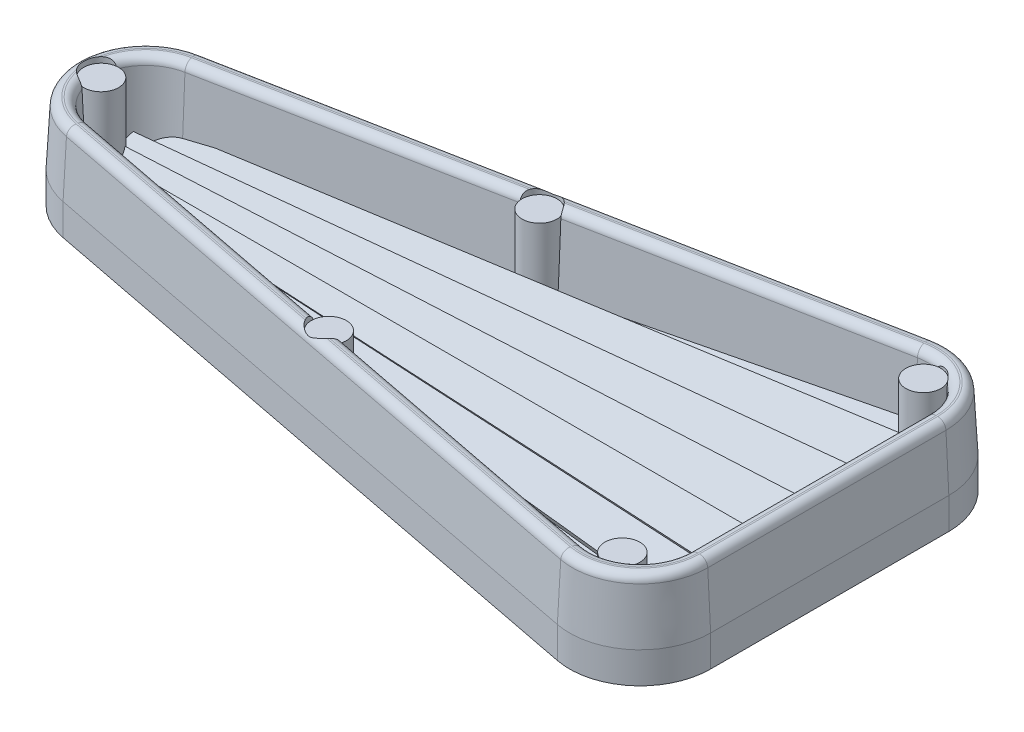
SolidWorks part; units mm, degrees
ref_plane "Front Plane" through (0, 0, 0) normal (0, 0, 1) x (1, 0, 0)
ref_plane "Top Plane" through (0, 0, 0) normal (0, 1, 0) x (1, 0, 0)
ref_plane "Right Plane" through (0, 0, 0) normal (1, 0, 0) x (0, 0, -1)
sketch "Sketch1" plane through (0, 0, 0) normal (0, 1, 0) x (1, 0, 0)
  line L0 (24.0776, 4.6752) -> (65.4796, 12.7143)
  line L1 (0, 0) -> (148.2111, 0) construction
  line L2 (71.1498, 8.0391) -> (71.1498, -8.0391)
  line L3 (24.0776, -4.6752) -> (65.4796, -12.7143)
  line L4 (0, 0) -> (85.7563, 4.4943) construction
  line L5 (0, 0) -> (80.0927, 8.4181) construction
  line L6 (0, 0) -> (103.5127, 16.3948) construction
  arc A0 (24.0776, 4.6752) -> (24.0776, -4.6752) centre (24.9853, 0) ccw
  arc A1 (71.1498, -8.0391) -> (65.4796, -12.7143) centre (66.3873, -8.0391) cw
  arc A2 (71.1498, 8.0391) -> (65.4796, 12.7143) centre (66.3873, 8.0391) ccw
  point P12 (71.1498, 0)
  dimension "D1" = 4.7625
  dimension "D2" = 4.7625
  dimension "D3" = 50.927
  dimension "D4" = 25.6032
  dimension "D5" = 3
  dimension "D6" = 6
  dimension "D7" = 9
extrude "Boss-Extrude1" add sketch "Sketch1" along normal blind 3.4544
sketch "Sketch2" plane through (0, 0, 0) normal (1, 0, 0) x (0, 0, -1)
  line L0 (0, 0) -> (0, 5.5486) construction
  line L1 (-1.905, 3.4544) -> (0, 1.5494)
  line L2 (-8.0391, 3.4544) -> (8.0391, 3.4544) construction
  line L3 (1.905, 3.4544) -> (0, 1.5494)
  line L4 (-1.905, 3.4544) -> (1.905, 3.4544)
  dimension "D1" = 90
  dimension "D2" = 3.81
extrude "Cut-Extrude1" cut sketch "Sketch2" along normal through all
ref_plane "Plane1" through (0, 0, 0) normal (0.9986, 0, -0.0523) x (-0.0523, 0, -0.9986)
sketch "Sketch3" plane through (0, 0, 0) normal (0.9986, 0, -0.0523) x (-0.0523, 0, -0.9986)
  line L0 (0, 0) -> (0, 11.5353) construction
  line L1 (3.4087, 3.4544) -> (0.8232, 3.4544) construction
  line L2 (1.905, 3.4544) -> (-1.905, 3.4544)
  line L3 (0, 1.5494) -> (1.905, 3.4544)
  line L4 (0, 1.5494) -> (-1.905, 3.4544)
  dimension "D1" = 90
  dimension "D2" = 3.81
extrude "Cut-Extrude2" cut sketch "Sketch3" along normal through all
ref_plane "Plane2" through (0, 0, 0) normal (0.9945, 0, -0.1045) x (-0.1045, 0, -0.9945)
sketch "Sketch4" plane through (0, 0, 0) normal (0.9945, 0, -0.1045) x (-0.1045, 0, -0.9945)
  line L0 (2.1328, 3.4544) -> (0.7805, 3.4544) construction
  line L1 (1.905, 3.4544) -> (-1.905, 3.4544)
  line L2 (0, 0) -> (0, 4.7652) construction
  line L3 (1.905, 3.4544) -> (0, 1.5494)
  line L4 (-1.905, 3.4544) -> (0, 1.5494)
  dimension "D1" = 90
  dimension "D2" = 3.81
extrude "Cut-Extrude3" cut sketch "Sketch4" along normal through all
ref_plane "Plane3" through (0, 0, 0) normal (0.9877, 0, -0.1564) x (-0.1564, 0, -0.9877)
sketch "Sketch5" plane through (0, 0, 0) normal (0.9877, 0, -0.1564) x (-0.1564, 0, -0.9877)
  line L0 (0, 0) -> (0, 3.7696) construction
  line L1 (0, 1.5494) -> (1.905, 3.4544)
  line L2 (2.3145, 3.4544) -> (0.8511, 3.4544) construction
  line L3 (1.905, 3.4544) -> (-1.905, 3.4544)
  line L4 (0, 1.5494) -> (-1.905, 3.4544)
  dimension "D1" = 90
  dimension "D2" = 3.81
extrude "Cut-Extrude4" cut sketch "Sketch5" along normal through all
mirror "Mirror1" about plane through (0, 0, 0) normal (0, 0, 1) of "Cut-Extrude4", "Cut-Extrude3", "Cut-Extrude2"
sketch "Sketch6" plane through (0, 0, 0) normal (0, -1, 0) x (1, 0, 0)
  line L3 (65.4796, 12.7143) -> (24.0776, 4.6752)
  line L4 (24.0776, -4.6752) -> (65.4796, -12.7143)
  line L5 (71.1498, -8.0391) -> (71.1498, 8.0391)
  line L6 (65.4796, 12.7143) -> (24.0776, 4.6752)
  line L7 (24.0776, -4.6752) -> (65.4796, -12.7143)
  line L8 (71.1498, -8.0391) -> (71.1498, 8.0391)
  arc A3 (71.1498, 8.0391) -> (65.4796, 12.7143) centre (66.3873, 8.0391) ccw
  arc A4 (24.0776, 4.6752) -> (24.0776, -4.6752) centre (24.9853, 0) ccw
  arc A5 (65.4796, -12.7143) -> (71.1498, -8.0391) centre (66.3873, -8.0391) ccw
  arc A6 (71.1498, 8.0391) -> (65.4796, 12.7143) centre (66.3873, 8.0391) ccw
  arc A7 (24.0776, 4.6752) -> (24.0776, -4.6752) centre (24.9853, 0) ccw
  arc A8 (65.4796, -12.7143) -> (71.1498, -8.0391) centre (66.3873, -8.0391) ccw
  dimension "D1" = 0
extrude "Extrude-Thin1" add sketch "Sketch6" against normal blind 6.35 thin thin type one direction reverse wall 1.7272
sketch "Sketch7" plane through (0, 0, 0) normal (0, 0, 1) x (1, 0, 0)
  line L0 (71.1498, 6.35) -> (71.1498, 0) construction
  line L1 (71.1498, 6.35) -> (71.1498, 2.1082)
  line L2 (70.9275, 6.35) -> (71.1498, 2.1082)
  line L3 (71.1498, 6.35) -> (65.4796, 6.35) construction
  line L4 (70.9275, 6.35) -> (71.1498, 6.35)
  line L5 (65.4796, 0) -> (71.1498, 0) construction
  dimension "D1" = 3
  dimension "D2" = 2.1082
sketch "Sketch8" plane through (0, 6.35, 0) normal (0, 1, 0) x (1, 0, 0)
  line L0 (65.4796, -12.7143) -> (24.0776, -4.6752) construction
  line L1 (65.4796, -12.7143) -> (24.0776, -4.6752)
  line L2 (24.0776, 4.6752) -> (65.4796, 12.7143) construction
  line L3 (71.1498, 8.0391) -> (71.1498, -8.0391) construction
  line L4 (24.0776, 4.6752) -> (65.4796, 12.7143)
  line L5 (71.1498, 8.0391) -> (71.1498, -8.0391)
  arc A0 (24.0776, 4.6752) -> (24.0776, -4.6752) centre (24.9853, 0) ccw construction
  arc A1 (71.1498, 8.0391) -> (65.4796, 12.7143) centre (66.3873, 8.0391) ccw construction
  arc A2 (65.4796, -12.7143) -> (71.1498, -8.0391) centre (66.3873, -8.0391) ccw construction
  arc A3 (24.0776, 4.6752) -> (24.0776, -4.6752) centre (24.9853, 0) ccw
  arc A4 (71.1498, 8.0391) -> (65.4796, 12.7143) centre (66.3873, 8.0391) ccw
  arc A5 (65.4796, -12.7143) -> (71.1498, -8.0391) centre (66.3873, -8.0391) ccw
sweep "Cut-Sweep1" cut profiles "Sketch7" path "Sketch8"
draft "Draft1" type of draft neutral plane draft angle 3 faces to draft 6 face at (42.9563, 3.4402, 6.5815) face at (68.0659, 3.6847, 9.8543) face at (69.4226, 2.9617, 0) face at (68.0659, 3.6847, -9.8543) face at (42.9563, 3.4402, -6.5815) face at (22.8216, 2.5389, 0) neutral plane through (66.3873, 0, 8.0391) neutral plane normal (0, -1, 0) reverse direction yes parameters "D1"=3
fillet "Fillet1" radius 0.5588 12 edges at (68.53, 6.35, 10.6378) (69.7554, 6.35, 0) (68.53, 6.35, -10.6378) (45.0443, 6.35, -7.3259) (21.6173, 6.35, 0) (69.2756, 6.35, 11.5421) (69.2756, 6.35, -11.5421) (44.8209, 6.35, -8.4765) (20.4451, 6.35, 0) (45.0443, 6.35, 7.3259) (44.8209, 6.35, 8.4765)
sketch "Sketch9" plane through (0, 6.35, 0) normal (0, 1, 0) x (1, 0, 0)
  line L0 (0, 0) -> (83.9079, 0) construction
  circle A0 centre (21.9696, 0) radius 1.1811
  circle A1 centre (44.45, -7.112) radius 1.1811
  circle A2 centre (67.31, -10.16) radius 1.1811
  circle A3 centre (44.45, 7.112) radius 1.1811
  circle A4 centre (67.31, 10.16) radius 1.1811
  dimension "D1" = 2.3622
  dimension "D2" = 21.9696
  dimension "D3" = 10.16
  dimension "D4" = 67.31
  dimension "D5" = 44.45
  dimension "D6" = 7.112
extrude "Boss-Extrude2" add sketch "Sketch9" against normal blind 5.08
sketch "Sketch10" plane through (0, 6.35, 0) normal (0, 1, 0) x (1, 0, 0)
  circle A0 centre (44.45, -7.112) radius 1.1811
  circle A1 centre (67.31, -10.16) radius 1.1811
  circle A2 centre (67.31, -10.16) radius 1.1811
  circle A3 centre (67.31, 10.16) radius 1.1811
  circle A4 centre (67.31, 10.16) radius 1.1811
  circle A5 centre (44.45, 7.112) radius 1.1811
  circle A6 centre (21.9696, 0) radius 1.1811
  dimension "D1" = 0
  dimension "D2" = 0
extrude "Cut-Extrude5" cut sketch "Sketch10" against normal blind 0.381
sketch "Sketch11 - Offset .005" plane through (0, 0, 0) normal (0, -1, 0) x (1, 0, 0)
  line L6 (65.4553, 12.839) -> (24.0533, 4.7999)
  line L7 (24.0533, -4.7999) -> (65.4553, -12.839)
  line L8 (71.2768, -8.0391) -> (71.2768, 8.0391)
  line L9 (65.4553, 12.839) -> (24.0533, 4.7999)
  line L10 (24.0533, -4.7999) -> (65.4553, -12.839)
  line L11 (71.2768, -8.0391) -> (71.2768, 8.0391)
  arc A6 (71.2768, 8.0391) -> (65.4553, 12.839) centre (66.3873, 8.0391) ccw
  arc A7 (24.0533, 4.7999) -> (24.0533, -4.7999) centre (24.9853, 0) ccw
  arc A8 (65.4553, -12.839) -> (71.2768, -8.0391) centre (66.3873, -8.0391) ccw
  arc A9 (71.2768, 8.0391) -> (65.4553, 12.839) centre (66.3873, 8.0391) ccw
  arc A10 (24.0533, 4.7999) -> (24.0533, -4.7999) centre (24.9853, 0) ccw
  arc A11 (65.4553, -12.839) -> (71.2768, -8.0391) centre (66.3873, -8.0391) ccw
  dimension "D1" = 0.127
